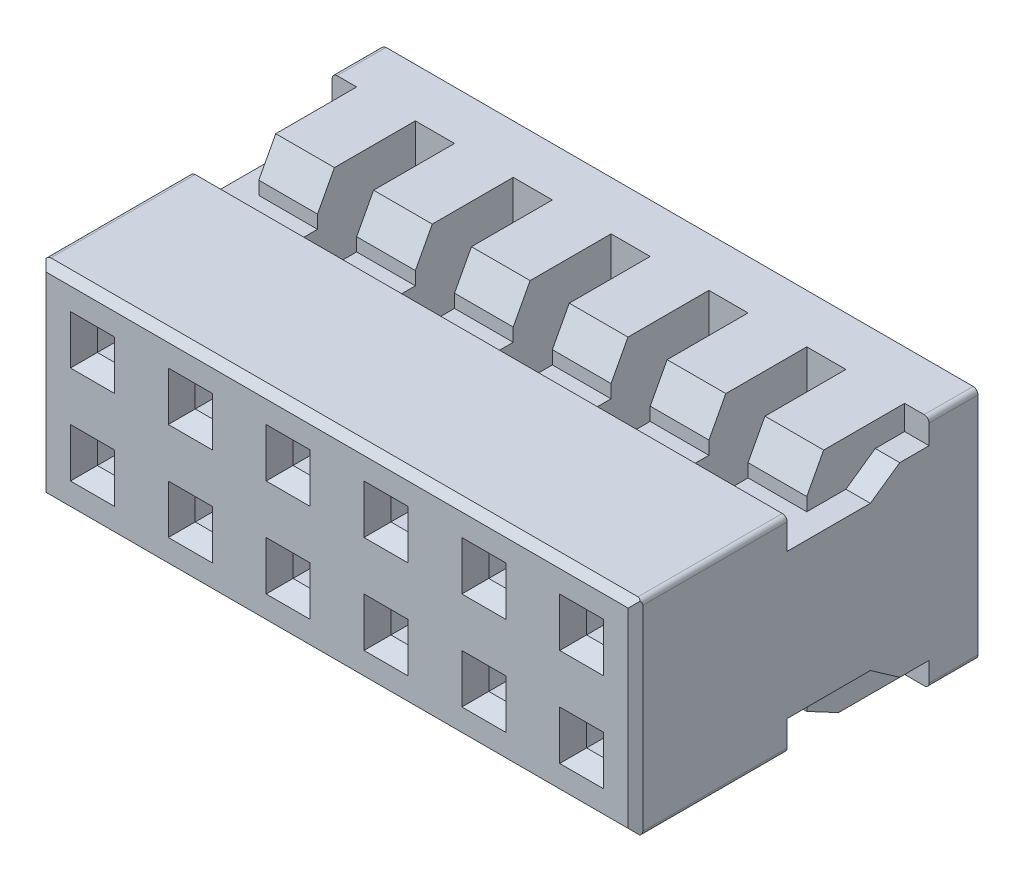
SolidWorks part; units mm, degrees
material "PVC Rigid"
ref_plane "Front Plane" through (0, 0, 0) normal (0, 0, 1) x (1, 0, 0)
ref_plane "Top Plane" through (0, 0, 0) normal (0, 1, 0) x (1, 0, 0)
ref_plane "Right Plane" through (0, 0, 0) normal (1, 0, 0) x (0, 0, -1)
ref_plane "Plane2" through (6.1, 0, 0) normal (1, 0, 0) x (0, 0, -1)
sketch "Sketch130" plane through (6.1, 0, 0) normal (1, 0, 0) x (0, 0, -1)
  line L0 (0, 2.4) -> (0, -2.4)
  line L1 (0, -2.4) -> (7, -2.4)
  line L2 (7, -2.4) -> (7, 2.4)
  line L3 (7, 2.4) -> (0, 2.4)
extrude "Extrude21" add sketch "Sketch130" against normal blind 12.2
sketch "Sketch131" plane through (6.1, 0, 0) normal (1, 0, 0) x (0, 0, -1)
  line L0 (4.8, -1.4799) -> (3.1, -1.4799)
  line L1 (3.1, -1.4799) -> (3.1, -2.4)
  line L2 (3.1, -2.4) -> (6, -2.4)
  line L3 (6, -2.4) -> (6, -1.9)
  line L4 (6, -1.9) -> (5.4, -1.9)
  line L5 (5.4, -1.9) -> (4.8, -1.4799)
extrude "Cut-Extrude110" cut sketch "Sketch131" against normal blind 0.5
sketch "Sketch132" plane through (6.1, 0, 0) normal (1, 0, 0) x (0, 0, -1)
  line L0 (6, 2.4) -> (3.1, 2.4)
  line L1 (3.1, 2.4) -> (3.1, 1.4799)
  line L2 (3.1, 1.4799) -> (4.8, 1.4799)
  line L3 (4.8, 1.4799) -> (5.4, 1.9)
  line L4 (5.4, 1.9) -> (6, 1.9)
  line L5 (6, 1.9) -> (6, 2.4)
extrude "Cut-Extrude111" cut sketch "Sketch132" against normal blind 0.5
sketch "Sketch133" plane through (-6.1, 0, 0) normal (-1, 0, 0) x (0, 0, 1)
  line L0 (-4.8, 1.4799) -> (-3.1, 1.4799)
  line L1 (-3.1, 1.4799) -> (-3.1, 2.4)
  line L2 (-3.1, 2.4) -> (-6, 2.4)
  line L3 (-6, 2.4) -> (-6, 1.9)
  line L4 (-6, 1.9) -> (-5.4, 1.9)
  line L5 (-5.4, 1.9) -> (-4.8, 1.4799)
extrude "Cut-Extrude112" cut sketch "Sketch133" against normal blind 0.5
sketch "Sketch134" plane through (-6.1, 0, 0) normal (-1, 0, 0) x (0, 0, 1)
  line L0 (-6, -2.4) -> (-3.1, -2.4)
  line L1 (-3.1, -2.4) -> (-3.1, -1.4799)
  line L2 (-3.1, -1.4799) -> (-4.8, -1.4799)
  line L3 (-4.8, -1.4799) -> (-5.4, -1.9)
  line L4 (-5.4, -1.9) -> (-6, -1.9)
  line L5 (-6, -1.9) -> (-6, -2.4)
extrude "Cut-Extrude113" cut sketch "Sketch134" against normal blind 0.5
sketch "Sketch135" plane through (0, 2.4, 0) normal (0, 1, 0) x (-1, 0, 0)
  line L0 (-3.6, -6) -> (-3.6, -3.1)
  line L1 (-3.6, -3.1) -> (-4.4, -3.1)
  line L2 (-4.4, -3.1) -> (-4.4, -6)
  line L3 (-4.4, -6) -> (-3.6, -6)
extrude "Cut-Extrude114" cut sketch "Sketch135" against normal blind 4.8
sketch "Sketch136" plane through (0, 2.4, 0) normal (0, 1, 0) x (-1, 0, 0)
  line L0 (-2.4, -6) -> (-1.6, -6)
  line L1 (-1.6, -6) -> (-1.6, -3.1)
  line L2 (-1.6, -3.1) -> (-2.4, -3.1)
  line L3 (-2.4, -3.1) -> (-2.4, -6)
extrude "Cut-Extrude115" cut sketch "Sketch136" against normal blind 4.8
sketch "Sketch137" plane through (0, 2.4, 0) normal (0, 1, 0) x (-1, 0, 0)
  line L0 (-0.4, -6) -> (0.4, -6)
  line L1 (0.4, -6) -> (0.4, -3.1)
  line L2 (0.4, -3.1) -> (-0.4, -3.1)
  line L3 (-0.4, -3.1) -> (-0.4, -6)
extrude "Cut-Extrude116" cut sketch "Sketch137" against normal blind 4.8
sketch "Sketch138" plane through (0, 2.4, 0) normal (0, 1, 0) x (-1, 0, 0)
  line L0 (1.6, -6) -> (2.4, -6)
  line L1 (2.4, -6) -> (2.4, -3.1)
  line L2 (2.4, -3.1) -> (1.6, -3.1)
  line L3 (1.6, -3.1) -> (1.6, -6)
extrude "Cut-Extrude117" cut sketch "Sketch138" against normal blind 4.8
sketch "Sketch139" plane through (0, 2.4, 0) normal (0, 1, 0) x (-1, 0, 0)
  line L0 (3.6, -6) -> (4.4, -6)
  line L1 (4.4, -6) -> (4.4, -3.1)
  line L2 (4.4, -3.1) -> (3.6, -3.1)
  line L3 (3.6, -3.1) -> (3.6, -6)
extrude "Cut-Extrude118" cut sketch "Sketch139" against normal blind 4.8
ref_plane "Plane3" through (0, 0, -3.1) normal (0, 0, 1) x (1, 0, 0)
sketch "Sketch140" plane through (0, 0, -3.1) normal (0, 0, 1) x (1, 0, 0)
  line L0 (4.4, -1.4799) -> (4.4, -2.4)
  line L1 (4.4, -2.4) -> (5.6, -2.4)
  line L2 (5.6, -2.4) -> (5.6, -1.4799)
  line L3 (5.6, -1.4799) -> (4.4, -1.4799)
extrude "Cut-Extrude119" cut sketch "Sketch140" against normal blind 0.9
ref_plane "Plane4" through (0, 0, -3.1) normal (0, 0, 1) x (1, 0, 0)
sketch "Sketch141" plane through (0, 0, -3.1) normal (0, 0, 1) x (1, 0, 0)
  line L0 (-5.6, -1.4799) -> (-5.6, -2.4)
  line L1 (-5.6, -2.4) -> (-4.4, -2.4)
  line L2 (-4.4, -2.4) -> (-4.4, -1.4799)
  line L3 (-4.4, -1.4799) -> (-5.6, -1.4799)
extrude "Cut-Extrude120" cut sketch "Sketch141" against normal blind 0.9
ref_plane "Plane5" through (0, 0, -3.1) normal (0, 0, 1) x (1, 0, 0)
sketch "Sketch142" plane through (0, 0, -3.1) normal (0, 0, 1) x (1, 0, 0)
  line L0 (5.6, 1.4799) -> (5.6, 2.4)
  line L1 (5.6, 2.4) -> (4.4, 2.4)
  line L2 (4.4, 2.4) -> (4.4, 1.4799)
  line L3 (4.4, 1.4799) -> (5.6, 1.4799)
extrude "Cut-Extrude121" cut sketch "Sketch142" against normal blind 0.9
ref_plane "Plane6" through (0, 0, -3.1) normal (0, 0, 1) x (1, 0, 0)
sketch "Sketch143" plane through (0, 0, -3.1) normal (0, 0, 1) x (1, 0, 0)
  line L0 (-4.4, 1.4799) -> (-4.4, 2.4)
  line L1 (-4.4, 2.4) -> (-5.6, 2.4)
  line L2 (-5.6, 2.4) -> (-5.6, 1.4799)
  line L3 (-5.6, 1.4799) -> (-4.4, 1.4799)
extrude "Cut-Extrude122" cut sketch "Sketch143" against normal blind 0.9
ref_plane "Plane7" through (0, 0, -3.1) normal (0, 0, -1) x (-1, 0, 0)
sketch "Sketch144" plane through (0, 0, -3.1) normal (0, 0, -1) x (-1, 0, 0)
  line L0 (-4.4, 1.4799) -> (-4.4, -1.4799)
  line L1 (-4.4, -1.4799) -> (-3.6, -1.4799)
  line L2 (-3.6, -1.4799) -> (-3.6, 1.4799)
  line L3 (-3.6, 1.4799) -> (-4.4, 1.4799)
extrude "Cut-Extrude123" cut sketch "Sketch144" against normal blind 2.85
sketch "Sketch145" plane through (0, 0, -3.1) normal (0, 0, -1) x (-1, 0, 0)
  line L0 (-2.4, 1.4799) -> (-2.4, -1.4799)
  line L1 (-2.4, -1.4799) -> (-1.6, -1.4799)
  line L2 (-1.6, -1.4799) -> (-1.6, 1.4799)
  line L3 (-1.6, 1.4799) -> (-2.4, 1.4799)
extrude "Cut-Extrude124" cut sketch "Sketch145" against normal blind 2.85
sketch "Sketch146" plane through (0, 0, -3.1) normal (0, 0, -1) x (-1, 0, 0)
  line L0 (-0.4, 1.4799) -> (-0.4, -1.4799)
  line L1 (-0.4, -1.4799) -> (0.4, -1.4799)
  line L2 (0.4, -1.4799) -> (0.4, 1.4799)
  line L3 (0.4, 1.4799) -> (-0.4, 1.4799)
extrude "Cut-Extrude125" cut sketch "Sketch146" against normal blind 2.85
sketch "Sketch147" plane through (0, 0, -3.1) normal (0, 0, -1) x (-1, 0, 0)
  line L0 (1.6, 1.4799) -> (1.6, -1.4799)
  line L1 (1.6, -1.4799) -> (2.4, -1.4799)
  line L2 (2.4, -1.4799) -> (2.4, 1.4799)
  line L3 (2.4, 1.4799) -> (1.6, 1.4799)
extrude "Cut-Extrude126" cut sketch "Sketch147" against normal blind 2.85
sketch "Sketch148" plane through (0, 0, -3.1) normal (0, 0, -1) x (-1, 0, 0)
  line L0 (3.6, 1.4799) -> (3.6, -1.4799)
  line L1 (3.6, -1.4799) -> (4.4, -1.4799)
  line L2 (4.4, -1.4799) -> (4.4, 1.4799)
  line L3 (4.4, 1.4799) -> (3.6, 1.4799)
extrude "Cut-Extrude127" cut sketch "Sketch148" against normal blind 2.85
sketch "Sketch149" plane through (0, -2.4, 0) normal (0, -1, 0) x (1, 0, 0)
  line L0 (6.1, -3.1) -> (6.1, 0)
  line L1 (6.1, 0) -> (-6.1, 0)
  line L2 (-6.1, 0) -> (-6.1, -3.1)
  line L3 (-6.1, -3.1) -> (-3.6, -3.1)
  line L4 (-3.6, -3.1) -> (-3.6, -4)
  line L5 (-3.6, -4) -> (-2.4, -4)
  line L6 (-2.4, -4) -> (-2.4, -3.1)
  line L7 (-2.4, -3.1) -> (-1.6, -3.1)
  line L8 (-1.6, -3.1) -> (-1.6, -4)
  line L9 (-1.6, -4) -> (-0.4, -4)
  line L10 (-0.4, -4) -> (-0.4, -3.1)
  line L11 (-0.4, -3.1) -> (0.4, -3.1)
  line L12 (0.4, -3.1) -> (0.4, -4)
  line L13 (0.4, -4) -> (1.6, -4)
  line L14 (1.6, -4) -> (1.6, -3.1)
  line L15 (1.6, -3.1) -> (2.4, -3.1)
  line L16 (2.4, -3.1) -> (2.4, -4)
  line L17 (2.4, -4) -> (3.6, -4)
  line L18 (3.6, -4) -> (3.6, -3.1)
  line L19 (3.6, -3.1) -> (6.1, -3.1)
extrude "Cut-Extrude128" cut sketch "Sketch149" against normal blind 0.3
sketch "Sketch150" plane through (0, 2.4, 0) normal (0, 1, 0) x (-1, 0, 0)
  line L0 (3.6, -3.1) -> (6.1, -3.1)
  line L1 (6.1, -3.1) -> (6.1, 0)
  line L2 (6.1, 0) -> (-6.1, 0)
  line L3 (-6.1, 0) -> (-6.1, -3.1)
  line L4 (-6.1, -3.1) -> (-3.6, -3.1)
  line L5 (-3.6, -3.1) -> (-3.6, -4)
  line L6 (-3.6, -4) -> (-2.4, -4)
  line L7 (-2.4, -4) -> (-2.4, -3.1)
  line L8 (-2.4, -3.1) -> (-1.6, -3.1)
  line L9 (-1.6, -3.1) -> (-1.6, -4)
  line L10 (-1.6, -4) -> (-0.4, -4)
  line L11 (-0.4, -4) -> (-0.4, -3.1)
  line L12 (-0.4, -3.1) -> (0.4, -3.1)
  line L13 (0.4, -3.1) -> (0.4, -4)
  line L14 (0.4, -4) -> (1.6, -4)
  line L15 (1.6, -4) -> (1.6, -3.1)
  line L16 (1.6, -3.1) -> (2.4, -3.1)
  line L17 (2.4, -3.1) -> (2.4, -4)
  line L18 (2.4, -4) -> (3.6, -4)
  line L19 (3.6, -4) -> (3.6, -3.1)
extrude "Cut-Extrude129" cut sketch "Sketch150" against normal blind 0.3
sketch "Sketch151" plane through (0, 0, -6) normal (0, 0, 1) x (1, 0, 0)
  line L0 (-4.4, 1.4799) -> (-4.4, 0.5598)
  line L1 (-4.4, 0.5598) -> (-3.6, 0.5598)
  line L2 (-3.6, 0.5598) -> (-3.6, 1.4799)
  line L3 (-3.6, 1.4799) -> (-4.4, 1.4799)
extrude "Cut-Extrude130" cut sketch "Sketch151" against normal blind 1
sketch "Sketch152" plane through (0, 0, -6) normal (0, 0, 1) x (1, 0, 0)
  line L0 (-2.4, 0.5598) -> (-1.6, 0.5598)
  line L1 (-1.6, 0.5598) -> (-1.6, 1.4799)
  line L2 (-1.6, 1.4799) -> (-2.4, 1.4799)
  line L3 (-2.4, 1.4799) -> (-2.4, 0.5598)
extrude "Cut-Extrude131" cut sketch "Sketch152" against normal blind 1
sketch "Sketch153" plane through (0, 0, -6) normal (0, 0, 1) x (1, 0, 0)
  line L0 (-0.4, 0.5598) -> (0.4, 0.5598)
  line L1 (0.4, 0.5598) -> (0.4, 1.4799)
  line L2 (0.4, 1.4799) -> (-0.4, 1.4799)
  line L3 (-0.4, 1.4799) -> (-0.4, 0.5598)
extrude "Cut-Extrude132" cut sketch "Sketch153" against normal blind 1
sketch "Sketch154" plane through (0, 0, -6) normal (0, 0, 1) x (1, 0, 0)
  line L0 (1.6, 0.5598) -> (2.4, 0.5598)
  line L1 (2.4, 0.5598) -> (2.4, 1.4799)
  line L2 (2.4, 1.4799) -> (1.6, 1.4799)
  line L3 (1.6, 1.4799) -> (1.6, 0.5598)
extrude "Cut-Extrude133" cut sketch "Sketch154" against normal blind 1
sketch "Sketch155" plane through (0, 0, -6) normal (0, 0, 1) x (1, 0, 0)
  line L0 (3.6, 0.5598) -> (4.4, 0.5598)
  line L1 (4.4, 0.5598) -> (4.4, 1.4799)
  line L2 (4.4, 1.4799) -> (3.6, 1.4799)
  line L3 (3.6, 1.4799) -> (3.6, 0.5598)
extrude "Cut-Extrude134" cut sketch "Sketch155" against normal blind 1
sketch "Sketch156" plane through (0, 0, -6) normal (0, 0, 1) x (1, 0, 0)
  line L0 (-3.6, 0.5598) -> (-3.6, -1.2805)
  line L1 (-3.6, -1.2805) -> (-4.4, -1.2805)
  line L2 (-4.4, -1.2805) -> (-4.4, 0.5598)
  line L3 (-4.4, 0.5598) -> (-3.6, 0.5598)
extrude "Extrude22" add sketch "Sketch156" along normal blind 1.2
sketch "Sketch157" plane through (0, 0, -6) normal (0, 0, 1) x (1, 0, 0)
  line L0 (-1.6, 0.5598) -> (-1.6, -1.2805)
  line L1 (-1.6, -1.2805) -> (-2.4, -1.2805)
  line L2 (-2.4, -1.2805) -> (-2.4, 0.5598)
  line L3 (-2.4, 0.5598) -> (-1.6, 0.5598)
extrude "Extrude23" add sketch "Sketch157" along normal blind 1.2
sketch "Sketch158" plane through (0, 0, -6) normal (0, 0, 1) x (1, 0, 0)
  line L0 (0.4, 0.5598) -> (0.4, -1.2805)
  line L1 (0.4, -1.2805) -> (-0.4, -1.2805)
  line L2 (-0.4, -1.2805) -> (-0.4, 0.5598)
  line L3 (-0.4, 0.5598) -> (0.4, 0.5598)
extrude "Extrude24" add sketch "Sketch158" along normal blind 1.2
sketch "Sketch159" plane through (0, 0, -6) normal (0, 0, 1) x (1, 0, 0)
  line L0 (2.4, 0.5598) -> (2.4, -1.2805)
  line L1 (2.4, -1.2805) -> (1.6, -1.2805)
  line L2 (1.6, -1.2805) -> (1.6, 0.5598)
  line L3 (1.6, 0.5598) -> (2.4, 0.5598)
extrude "Extrude25" add sketch "Sketch159" along normal blind 1.2
sketch "Sketch160" plane through (0, 0, -6) normal (0, 0, 1) x (1, 0, 0)
  line L0 (4.4, 0.5598) -> (4.4, -1.2805)
  line L1 (4.4, -1.2805) -> (3.6, -1.2805)
  line L2 (3.6, -1.2805) -> (3.6, 0.5598)
  line L3 (3.6, 0.5598) -> (4.4, 0.5598)
extrude "Extrude26" add sketch "Sketch160" along normal blind 1.2
sketch "Sketch161" plane through (0, 0, -6) normal (0, 0, 1) x (1, 0, 0)
  line L0 (-4.4, -1.4799) -> (-3.6, -1.4799)
  line L1 (-3.6, -1.4799) -> (-3.6, -1.2805)
  line L2 (-3.6, -1.2805) -> (-4.4, -1.2805)
  line L3 (-4.4, -1.2805) -> (-4.4, -1.4799)
extrude "Cut-Extrude135" cut sketch "Sketch161" against normal blind 1
pattern_linear "LPattern13" count 5 spacing 2 along (1, 0, 0) of "Cut-Extrude135"
sketch "Sketch162" plane through (0, -2.1, 0) normal (0, -1, 0) x (1, 0, 0)
  line L0 (-3.6, -3.1) -> (-3.6, -4)
  line L1 (-3.6, -4) -> (-2.4, -4)
  line L2 (-2.4, -4) -> (-2.4, -3.1)
  line L3 (-2.4, -3.1) -> (-3.6, -3.1)
extrude "Cut-Extrude136" cut sketch "Sketch162" against normal blind 0.6201
sketch "Sketch163" plane through (0, -2.1, 0) normal (0, -1, 0) x (1, 0, 0)
  line L0 (-1.6, -3.1) -> (-1.6, -4)
  line L1 (-1.6, -4) -> (-0.4, -4)
  line L2 (-0.4, -4) -> (-0.4, -3.1)
  line L3 (-0.4, -3.1) -> (-1.6, -3.1)
extrude "Cut-Extrude137" cut sketch "Sketch163" against normal blind 0.6201
sketch "Sketch164" plane through (0, -2.1, 0) normal (0, -1, 0) x (1, 0, 0)
  line L0 (0.4, -3.1) -> (0.4, -4)
  line L1 (0.4, -4) -> (1.6, -4)
  line L2 (1.6, -4) -> (1.6, -3.1)
  line L3 (1.6, -3.1) -> (0.4, -3.1)
extrude "Cut-Extrude138" cut sketch "Sketch164" against normal blind 0.6201
sketch "Sketch165" plane through (0, -2.1, 0) normal (0, -1, 0) x (1, 0, 0)
  line L0 (2.4, -3.1) -> (2.4, -4)
  line L1 (2.4, -4) -> (3.6, -4)
  line L2 (3.6, -4) -> (3.6, -3.1)
  line L3 (3.6, -3.1) -> (2.4, -3.1)
extrude "Cut-Extrude139" cut sketch "Sketch165" against normal blind 0.6201
sketch "Sketch166" plane through (0, 2.1, 0) normal (0, 1, 0) x (-1, 0, 0)
  line L0 (-2.4, -4) -> (-2.4, -3.1)
  line L1 (-2.4, -3.1) -> (-3.6, -3.1)
  line L2 (-3.6, -3.1) -> (-3.6, -4)
  line L3 (-3.6, -4) -> (-2.4, -4)
extrude "Cut-Extrude140" cut sketch "Sketch166" against normal blind 0.6201
sketch "Sketch167" plane through (0, 2.1, 0) normal (0, 1, 0) x (-1, 0, 0)
  line L0 (-0.4, -4) -> (-0.4, -3.1)
  line L1 (-0.4, -3.1) -> (-1.6, -3.1)
  line L2 (-1.6, -3.1) -> (-1.6, -4)
  line L3 (-1.6, -4) -> (-0.4, -4)
extrude "Cut-Extrude141" cut sketch "Sketch167" against normal blind 0.6201
sketch "Sketch168" plane through (0, 2.1, 0) normal (0, 1, 0) x (-1, 0, 0)
  line L0 (1.6, -4) -> (1.6, -3.1)
  line L1 (1.6, -3.1) -> (0.4, -3.1)
  line L2 (0.4, -3.1) -> (0.4, -4)
  line L3 (0.4, -4) -> (1.6, -4)
extrude "Cut-Extrude142" cut sketch "Sketch168" against normal blind 0.6201
sketch "Sketch169" plane through (0, 2.1, 0) normal (0, 1, 0) x (-1, 0, 0)
  line L0 (3.6, -4) -> (3.6, -3.1)
  line L1 (3.6, -3.1) -> (2.4, -3.1)
  line L2 (2.4, -3.1) -> (2.4, -4)
  line L3 (2.4, -4) -> (3.6, -4)
extrude "Cut-Extrude143" cut sketch "Sketch169" against normal blind 0.6201
chamfer "Chamfer85" distance 0.4201 angle 55 1 edges at (4, -1.2805, -4.8)
chamfer "Chamfer86" distance 0.4201 angle 55 1 edges at (2, -1.2805, -4.8)
chamfer "Chamfer87" distance 0.4201 angle 55 1 edges at (0, -1.2805, -4.8)
chamfer "Chamfer88" distance 0.4201 angle 55 1 edges at (-2, -1.2805, -4.8)
chamfer "Chamfer89" distance 0.4201 angle 55 1 edges at (-4, -1.2805, -4.8)
chamfer "Chamfer90" distance 0.6 angle 35 1 edges at (4, 0.5598, -4.8)
chamfer "Chamfer91" distance 0.6 angle 35 1 edges at (2, 0.5598, -4.8)
chamfer "Chamfer92" distance 0.6 angle 35 1 edges at (0, 0.5598, -4.8)
chamfer "Chamfer93" distance 0.6 angle 35 1 edges at (-2, 0.5598, -4.8)
chamfer "Chamfer94" distance 0.6 angle 35 1 edges at (-4, 0.5598, -4.8)
chamfer "Chamfer95" distance 0.3456 angle 62 6 edges at (5, -2.4, -4) (3, -2.4, -4) (1, -2.4, -4) (-1, -2.4, -4) (-3, -2.4, -4) (-5, -2.4, -4)
chamfer "Chamfer96" distance 0.65 angle 28 6 edges at (-5, 2.4, -4) (-3, 2.4, -4) (-1, 2.4, -4) (1, 2.4, -4) (3, 2.4, -4) (5, 2.4, -4)
sketch "Sketch170" plane through (0, 0, 0) normal (0, 0, 1) x (1, 0, 0)
  line L0 (4.75, 0.7) -> (5.25, 0.7)
  line L1 (5.25, 0.7) -> (5.25, 1.3)
  line L2 (5.25, 1.3) -> (4.75, 1.3)
  line L3 (4.75, 1.3) -> (4.75, 0.7)
extrude "Cut-Extrude144" cut sketch "Sketch170" against normal blind 7
chamfer "Chamfer97" distance 0.2 angle 60.255 4 edges at (5, 1.3, 0) (5.25, 1, 0) (4.75, 1, 0) (5, 0.7, 0)
chamfer "Chamfer98" distance 0.15 angle 45 4 edges at (-6.1, 0, 0) (0, 2.1, 0) (0, -2.1, 0) (6.1, 0, 0)
fillet "Fillet13" radius 0.1 4 edges at (-6.1, -2.4, -6.5) (-6.1, 2.4, -6.5) (6.1, -2.4, -6.5) (6.1, 2.4, -6.5)
fillet "Fillet14" radius 0.1 4 edges at (-6.1, -2.1, -1.625) (-6.1, 2.1, -1.625) (6.1, 2.1, -1.625) (6.1, -2.1, -1.625)
pattern_linear "LPattern14" count 6 spacing 2 along (-1, 0, 0) count 2 spacing 2 along (0, -1, 0) of "Cut-Extrude144", "Chamfer97"
